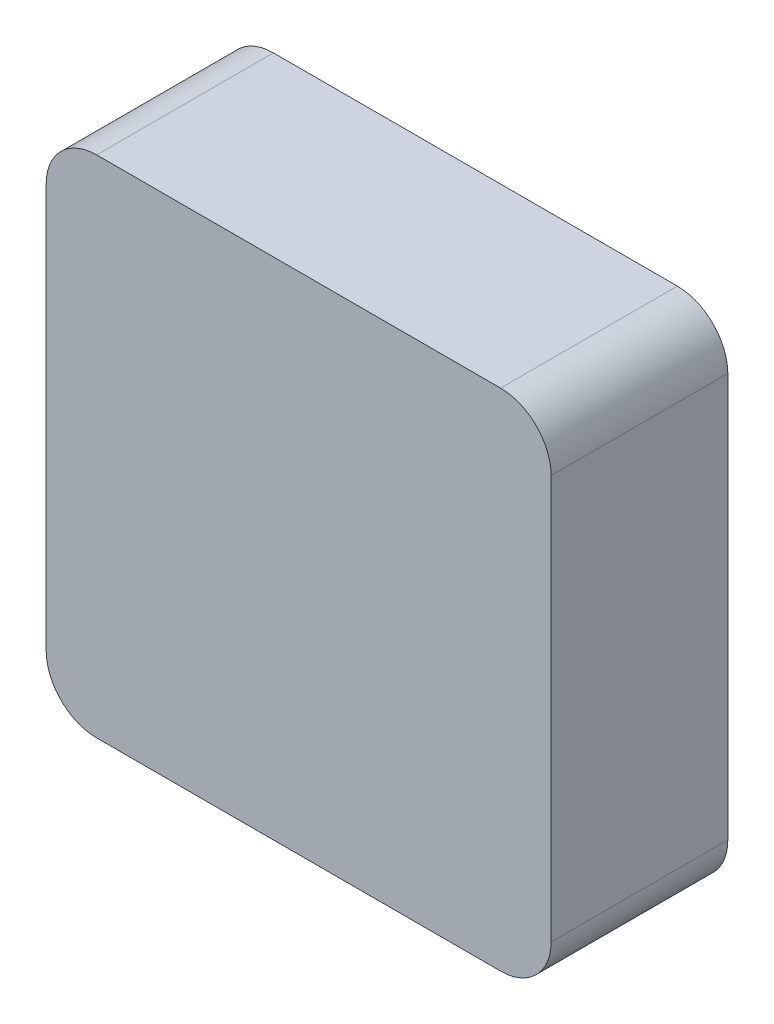
SolidWorks part; units mm, degrees
material "Duranickel(R) 301"
ref_plane "前视基准面" through (0, 0, 0) normal (0, 0, 1) x (1, 0, 0)
ref_plane "上视基准面" through (0, 0, 0) normal (0, 1, 0) x (1, 0, 0)
ref_plane "右视基准面" through (0, 0, 0) normal (1, 0, 0) x (0, 0, -1)
other "Configuration Table"
sketch "Sketch1" plane through (0, 0, 0) normal (0, 0, 1) x (1, 0, 0)
  line L1 (0, 0) -> (100, 0)
  line L2 (0, 0) -> (0, 100)
  line L3 (0, 100) -> (100, 100)
  line L4 (100, 0) -> (100, 100)
  dimension "D1" = 100
  dimension "D2" = 100
extrude "Boss-Extrude1" add sketch "Sketch1" along normal blind 35
fillet "Fillet1" radius 10 4 edges at (0, 100, 17.5) (0, 0, 17.5) (100, 0, 17.5) (100, 100, 17.5)
sketch "Sketch2" plane through (0, 0, 0) normal (0, -1, 0) x (1, 0, 0)
  line L0 (10, 35) -> (10, 0) construction
  line L1 (39.6464, 18.4261) -> (49.0501, 18.4261)
  line L2 (39.6464, 18.4261) -> (39.6464, 14.0567)
  line L3 (39.6464, 14.0567) -> (49.0501, 14.0567)
  line L4 (49.0501, 18.4261) -> (49.0501, 14.0567)
  line L5 (19.2242, 22.938) -> (30.1952, 22.938)
  line L6 (19.2242, 22.938) -> (19.2242, 14.1517)
  line L7 (19.2242, 14.1517) -> (30.1952, 14.1517)
  line L8 (30.1952, 22.938) -> (30.1952, 14.1517)
  line L9 (69.0449, 17.4288) -> (80.3009, 17.4288)
  line L10 (69.0449, 17.4288) -> (69.0449, 14.3417)
  line L11 (69.0449, 14.3417) -> (80.3009, 14.3417)
  line L12 (80.3009, 17.4288) -> (80.3009, 14.3417)
  line L13 (55.3668, 17.1913) -> (65.3879, 17.1913)
  line L14 (55.3668, 17.1913) -> (55.3668, 14.1517)
  line L15 (55.3668, 14.1517) -> (65.3879, 14.1517)
  line L16 (65.3879, 17.1913) -> (65.3879, 14.1517)
  line L17 (10, 35) -> (90, 35) construction
  dimension "D1" = 9.2242
  dimension "D2" = 20.1952
  dimension "D3" = 29.6464
  dimension "D4" = 39.0501
  dimension "D5" = 45.3668
  dimension "D6" = 55.3879
  dimension "D7" = 59.0449
  dimension "D8" = 70.3009
  dimension "D9" = 12.062
  dimension "D10" = 16.5739
  dimension "D11" = 17.5712
  dimension "D12" = 17.8087
  dimension "D13" = 20.6583
  dimension "D14" = 20.9433
  dimension "D19" = 20.8483
  dimension "D20" = 20.8483
extrude "Cut-Extrude1" cut sketch "Sketch2" against normal blind 5
